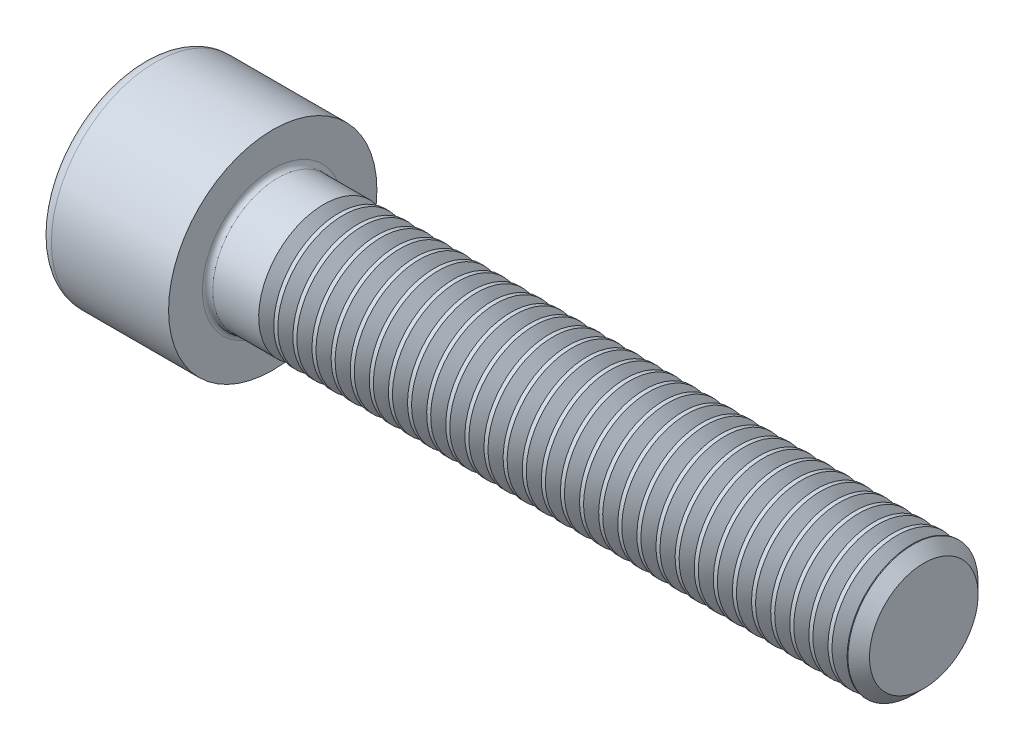
SolidWorks part; units mm, degrees
revolve "Base-Revolve" add sketch "BodySke"
sketch "BodySke" plane through (0, 0, 0) normal (0, 0, 1) x (1, 0, 0)
  line L0 (0, 0) -> (0, 8)
  line L1 (0, 8) -> (10, 8)
  line L2 (10, 8) -> (10, 5)
  line L3 (10, 5) -> (59.172, 5)
  line L4 (60, 4.172) -> (60, 0)
  line L5 (60, 0) -> (0, 0)
  line L6 (-31.75, 0) -> (127, 0) construction
  line L8 (60, 4.172) -> (59.172, 5)
  line L10 (60, -4.172) -> (59.172, -5) construction
  line L11 (11.5, 9.525) -> (11.5, 3.175) construction
  line L12 (10, 9.525) -> (10, 3.175) construction
  line L13 (0, 9.525) -> (0, 3.175) construction
cosmetic thread "ThreadCosmetic" [suppressed]
fillet "Fillet1" radius 0.4 1 edges at (10, 0, 5)
fillet "Fillet2" radius 1 1 edges at (0, 0, 8)
ref_plane "Plane1" through (0, 0, 0) normal (0, 0, 1) x (1, 0, 0)
ref_plane "Plane2" through (0, 0, 0) normal (0, 1, 0) x (1, 0, 0)
ref_plane "Plane3" through (0, 0, 0) normal (1, 0, 0) x (0, 0, -1)
sketch "Sketch2" plane through (0, 0, 0) normal (0, 0, 1) x (1, 0, 0)
  line L0 (0, 4.0125) -> (5, 4.0125)
  line L1 (5, 4.0125) -> (7.3166, 0)
  line L2 (-31.75, 0) -> (127, 0) construction
  line L3 (7.3166, 0) -> (0, 0)
  line L4 (0, 0) -> (0, 4.0125)
  line L6 (0, 0) -> (47.625, 0) construction
revolve "Hex-PreBroach" cut sketch "Sketch2" angle 360 about L6
sketch "Sketch3" plane through (0, 0, 0) normal (-1, 0, 0) x (0, 0.5, 0.866)
  line L0 (2.3166, 4.0125) -> (-2.3166, 4.0125)
  line L1 (-2.3166, 4.0125) -> (-4.6332, 0)
  line L2 (2.3166, 4.0125) -> (4.6332, 0)
  line L3 (2.3166, -4.0125) -> (4.6332, 0)
  line L4 (2.3166, -4.0125) -> (-2.3166, -4.0125)
  line L5 (-2.3166, -4.0125) -> (-4.6332, 0)
extrude "Hex" cut sketch "Sketch3" against normal blind 5
sketch "ThdSchSke" plane through (0, 0, 0) normal (0, 0, 1) x (1, 0, 0)
  line L0 (14.5, -4.172) -> (13.9202, -5)
  line L1 (14.5, -4.172) -> (15.0798, -5)
  line L2 (15.0798, -5) -> (15.0798, -6.25)
  line L3 (-3.175, 0) -> (5.1513, 0) construction
  line L4 (0, 7) -> (0, -7) construction
  line L5 (15.0798, -6.25) -> (13.9202, -6.25)
  line L6 (13.9202, -6.25) -> (13.9202, -5)
revolve "ThreadSchematic" cut sketch "ThdSchSke" angle 360 about L3
pattern_linear "ThdSchPat" count 31 spacing 1.4677 along (1, 0, 0) of "ThreadSchematic"
equation "\"D2@Sketch3\" = \"Hex_size@Sketch3\" / 2"
equation "\"D1@Sketch3\" = \"Hex_size@Sketch3\" / 2"
equation "\"D1@Sketch2\" = \"Hex_size@Sketch3\" / 2"
equation "\"Thread_minor@ThreadCosmetic\"  =  \"Minor_dia@BodySke\""
equation "\"Depth@Sketch2\" =  \"Key_eng@Hex\""
equation "\"Thread_length@ThreadCosmetic\" = ((sgn( (\"Length@BodySke\" - \"Advance@BodySke\" * 3.0) - \"Thread_nom@BodySke\" )-1)*( (\"Length@BodySke\" - \"Advance@BodySke\" * 3.0) - \"Thread_nom@BodySke\" ))/-2+ \"Thread_nom@BodySke\""
equation "\"Thread_minor@ThdSchSke\" = \"Minor_dia@BodySke\""
equation "\"Diameter@ThdSchSke\" = \"Diameter@BodySke\""
equation "\"Overcut@ThdSchSke\" = \"Diameter@BodySke\" * 1.25"
equation "\"Start@ThdSchSke\" = \"Head_ht@BodySke\" + \"Length@BodySke\" - \"Thread_length@ThreadCosmetic\"  '---Non-countersunk---"
equation "\"Num_threads@ThdSchPat\" = int( \"Thread_length@ThreadCosmetic\" / \"Advance@BodySke\" + 0.999 )  + 1"
equation "\"Advance@ThdSchPat\" = \"Thread_length@ThreadCosmetic\" /  (\"Num_threads@ThdSchPat\" - 1) 'relax it"
equation "\"Num_threads@ThdSchPat\" = \"Num_threads@ThdSchPat\" - sgn( \"Num_threads@ThdSchPat\" - 1) '---chamfered tips only---"
